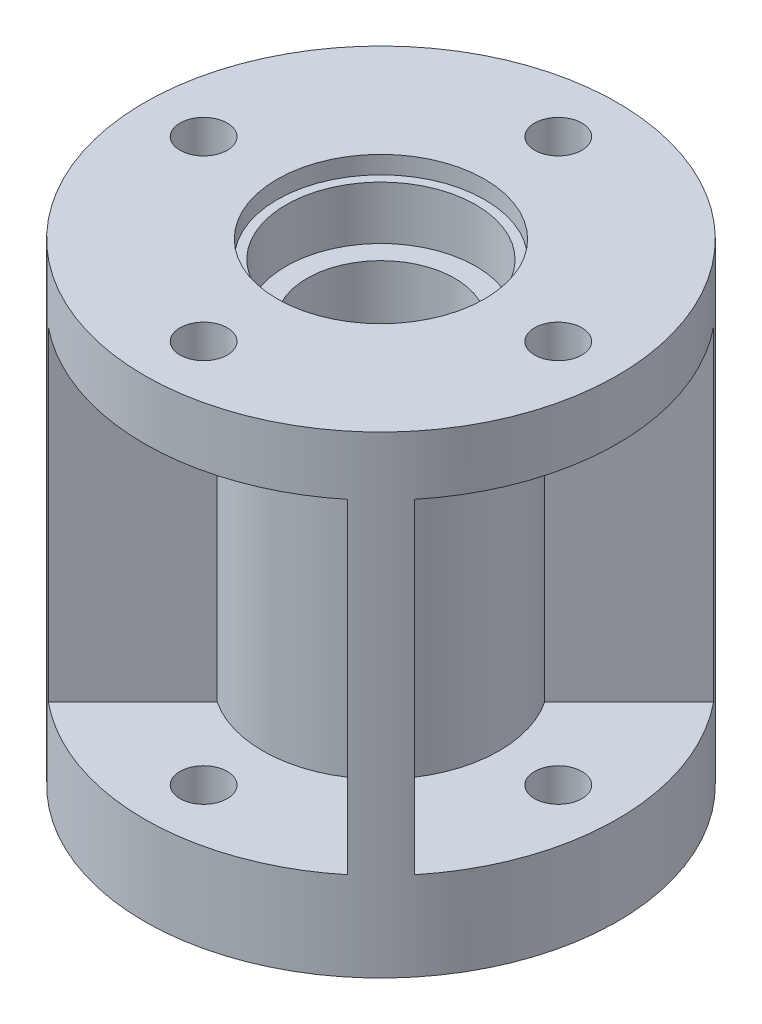
SolidWorks part; units mm, degrees
ref_plane "Front Plane" through (0, 0, 0) normal (0, 0, 1) x (1, 0, 0)
ref_plane "Top Plane" through (0, 0, 0) normal (0, 1, 0) x (1, 0, 0)
ref_plane "Right Plane" through (0, 0, 0) normal (1, 0, 0) x (0, 0, -1)
sketch "Sketch1" plane through (0, 0, 0) normal (0, 1, 0) x (1, 0, 0)
  circle A0 centre (0, 0) radius 12.5
  circle A1 centre (0, 0) radius 40
  dimension "D1" = 25
  dimension "D2" = 80
extrude "Boss-Extrude1" add sketch "Sketch1" along normal blind 15
sketch "Sketch3" plane through (0, 15, 0) normal (0, 1, 0) x (1, 0, 0)
  circle A0 centre (0, 0) radius 12.5
  circle A1 centre (0, 0) radius 20
  circle A2 centre (0, 0) radius 12.5 construction
  dimension "D1" = 40
extrude "Boss-Extrude2" add sketch "Sketch3" along normal blind 53
sketch "Sketch4" plane through (0, 68, 0) normal (0, 1, 0) x (1, 0, 0)
  circle A0 centre (0, 0) radius 16.05
  circle A1 centre (0, 0) radius 20
  circle A2 centre (0, 0) radius 20 construction
  dimension "D1" = 32.1
extrude "Boss-Extrude3" add sketch "Sketch4" along normal blind 12
sketch "Sketch5" plane through (0, 15, 0) normal (0, 1, 0) x (1, 0, 0)
  line L0 (0, 0) -> (-28.2843, -28.2843) construction
  line L1 (0, 0) -> (-24.4998, 0) construction
  line L2 (-16.6848, -11.028) -> (-30.9709, -25.3141)
  line L3 (-11.028, -16.6848) -> (-25.3141, -30.9709)
  line L4 (-16.6848, 11.028) -> (-30.9709, 25.3141)
  line L5 (-11.028, 16.6848) -> (-25.3141, 30.9709)
  line L6 (11.028, 16.6848) -> (25.3141, 30.9709)
  line L7 (16.6848, 11.028) -> (30.9709, 25.3141)
  line L8 (16.6848, -11.028) -> (30.9709, -25.3141)
  line L9 (11.028, -16.6848) -> (25.3141, -30.9709)
  arc A0 (-16.6848, -11.028) -> (-11.028, -16.6848) centre (0, 0) ccw
  circle A1 centre (0, 0) radius 20 construction
  arc A2 (-30.9709, -25.3141) -> (-25.3141, -30.9709) centre (0, 0) ccw
  circle A3 centre (0, 0) radius 40 construction
  arc A4 (-25.3141, 30.9709) -> (-30.9709, 25.3141) centre (0, 0) ccw
  arc A5 (-11.028, 16.6848) -> (-16.6848, 11.028) centre (0, 0) ccw
  arc A6 (30.9709, 25.3141) -> (25.3141, 30.9709) centre (0, 0) ccw
  arc A7 (16.6848, 11.028) -> (11.028, 16.6848) centre (0, 0) ccw
  arc A8 (25.3141, -30.9709) -> (30.9709, -25.3141) centre (0, 0) ccw
  arc A9 (11.028, -16.6848) -> (16.6848, -11.028) centre (0, 0) ccw
  point P10 (-14.1421, -14.1421)
  point P28 (0, 0)
  dimension "D1" = 45
  dimension "D2" = 8
  dimension "D3" = 4
extrude "Boss-Extrude4" add sketch "Sketch5" along normal up to surface (65 mm away) up to face at (0, 80, 20)
sketch "Sketch6" plane through (0, 80, 0) normal (0, 1, 0) x (1, 0, 0)
  circle A0 centre (0, 0) radius 17.55
  dimension "D1" = 35.1
extrude "Cut-Extrude2" cut sketch "Sketch6" against normal blind 3
sketch "Sketch7" plane through (0, 80, 0) normal (0, 1, 0) x (1, 0, 0)
  circle A0 centre (0, 0) radius 40
  circle A1 centre (0, 0) radius 20
  arc A2 (-25.3141, 30.9709) -> (-30.9709, 25.3141) centre (0, 0) ccw construction
  arc A3 (-16.6848, 11.028) -> (-16.6848, -11.028) centre (0, 0) ccw construction
extrude "Boss-Extrude5" add sketch "Sketch7" against normal blind 10
sketch "Sketch2" plane through (0, 0, 0) normal (0, 1, 0) x (1, 0, 0)
  circle A0 centre (0, 30) radius 4
  circle A1 centre (30, 0) radius 4
  circle A2 centre (0, -30) radius 4
  circle A3 centre (-30, 0) radius 4
  point P12 (0, 0)
  dimension "D1" = 8
  dimension "D2" = 30
  dimension "D3" = 4
extrude "Cut-Extrude1" cut sketch "Sketch2" along normal up to surface (80 mm away) up to face at (0, 80, 40)
